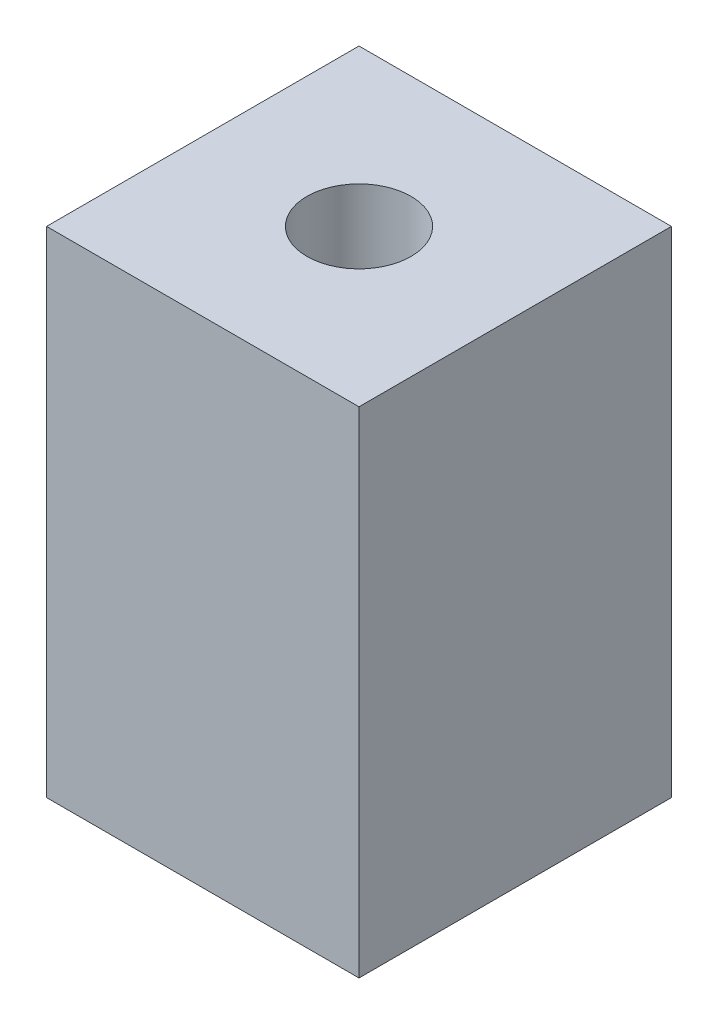
SolidWorks part; units mm, degrees
material "Pine"
ref_plane "Front Plane" through (0, 0, 0) normal (0, 0, 1) x (1, 0, 0)
ref_plane "Top Plane" through (0, 0, 0) normal (0, 1, 0) x (1, 0, 0)
ref_plane "Right Plane" through (0, 0, 0) normal (1, 0, 0) x (0, 0, -1)
sketch "Sketch1" plane through (0, 0, 0) normal (0, 1, 0) x (1, 0, 0)
  line L1 (-6, 6) -> (6, 6)
  line L2 (-6, 6) -> (-6, -6)
  line L3 (-6, -6) -> (6, -6)
  line L4 (6, 6) -> (6, -6)
  circle A0 centre (0, 0) radius 2
  point P0 (0, 0)
  point P6 (0, 0)
  dimension "D5" = 4
  dimension "D1" = 12
  dimension "D2" = 12
extrude "Boss-Extrude1" add sketch "Sketch1" along normal blind 19
